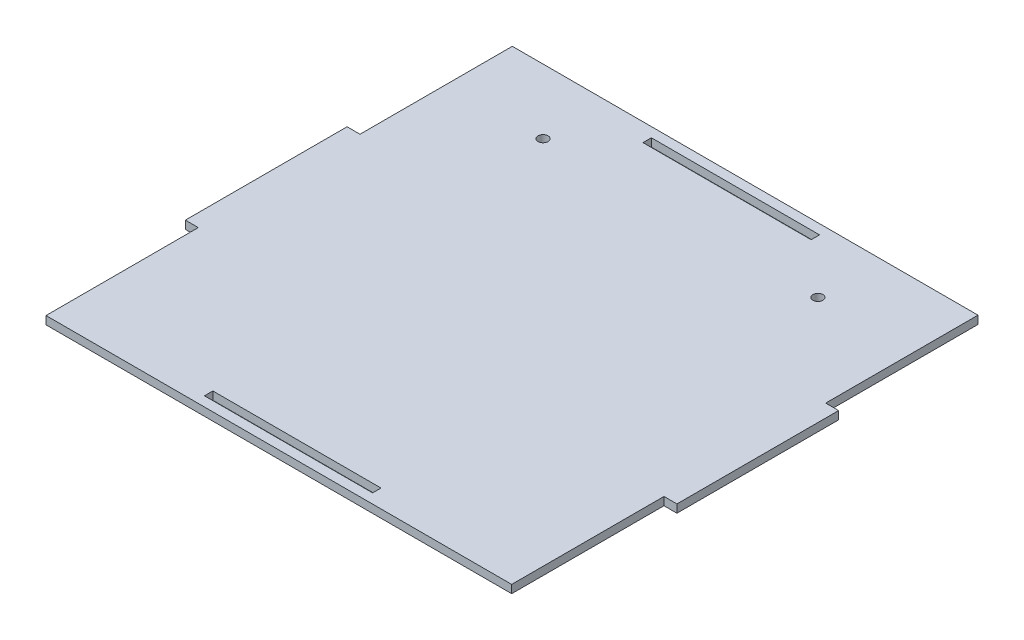
SolidWorks part; units mm, degrees
ref_plane "Front Plane" through (0, 0, 0) normal (0, 0, 1) x (1, 0, 0)
ref_plane "Top Plane" through (0, 0, 0) normal (0, 1, 0) x (1, 0, 0)
ref_plane "Right Plane" through (0, 0, 0) normal (1, 0, 0) x (0, 0, -1)
sketch "Sketch1" plane through (0, 0, 0) normal (0, 1, 0) x (1, 0, 0)
  line L4 (72, -25) -> (76, -25)
  line L5 (76, -25) -> (76, 25)
  line L6 (76, 25) -> (72, 25)
  line L7 (72, 25) -> (72, 72.1)
  line L8 (72, 72.1) -> (-72, 72.1)
  line L9 (-72, 72.1) -> (-72, 25)
  line L10 (-72, 25) -> (-76, 25)
  line L11 (-76, 25) -> (-76, -25)
  line L12 (-76, -25) -> (-72, -25)
  line L13 (-72, -25) -> (-72, -72.1)
  line L14 (-72, -72.1) -> (72, -72.1)
  line L15 (72, -72.1) -> (72, -25)
  line L16 (26, -69.1) -> (26, -66.5)
  line L17 (-26, -69.1) -> (26, -69.1)
  line L18 (-26, -69.1) -> (-26, -66.5)
  line L19 (-26, -66.5) -> (26, -66.5)
  line L20 (-76, 0) -> (76, 0) construction
  line L21 (0, 72.1) -> (0, -72.1) construction
  line L22 (-26, 69.1) -> (26, 69.1)
  line L23 (-26, 69.1) -> (-26, 66.5)
  line L24 (-26, 66.5) -> (26, 66.5)
  line L25 (26, 69.1) -> (26, 66.5)
  point P24 (0, 0)
  dimension "D1" = 52
  dimension "D2" = 3
  dimension "D3" = 26
  dimension "D4" = 4
  dimension "D5" = 50
  dimension "D6" = 4
  dimension "D7" = 50
  dimension "D8" = 47.1
  dimension "D9" = 47.1
  dimension "D10" = 47.1
  dimension "D11" = 72
  dimension "D12" = 4
  dimension "D13" = 4
extrude "Boss-Extrude1" add sketch "Sketch1" along normal blind 2.5
sketch "Sketch2" plane through (0, 2.5, 0) normal (0, 1, 0) x (1, 0, 0)
  line L12 (72, -72.1) -> (72, -25)
  line L13 (72, -25) -> (76, -25)
  line L14 (76, -25) -> (76, 25)
  line L15 (76, 25) -> (72, 25)
  line L16 (72, 25) -> (72, 72.1)
  line L17 (72, 72.1) -> (-72, 72.1)
  line L18 (-72, 72.1) -> (-72, 25)
  line L19 (-72, 25) -> (-76, 25)
  line L20 (-76, 25) -> (-76, -25)
  line L21 (-76, -25) -> (-72, -25)
  line L22 (-72, -25) -> (-72, -72.1)
  line L23 (-72, -72.1) -> (72, -72.1)
  line L24 (72, -72.1) -> (72, -25)
  line L25 (72, -25) -> (76, -25)
  line L26 (76, -25) -> (76, 25)
  line L27 (76, 25) -> (72, 25)
  line L28 (72, 25) -> (72, 72.1)
  line L29 (72, 72.1) -> (-72, 72.1)
  line L30 (-72, 72.1) -> (-72, 25)
  line L31 (-72, 25) -> (-76, 25)
  line L32 (-76, 25) -> (-76, -25)
  line L33 (-76, -25) -> (-72, -25)
  line L34 (-72, -25) -> (-72, -72.1)
  line L35 (-72, -72.1) -> (72, -72.1)
  circle A0 centre (42.5, 52.1) radius 1.55
  circle A1 centre (-42.5, 52.1) radius 1.55
  dimension "D2" = 3.1
  dimension "D3" = 29.5
  dimension "D4" = 20
  dimension "D1" = 0
extrude "Cut-Extrude1" cut sketch "Sketch2" against normal blind 10 contours A1 | A0
